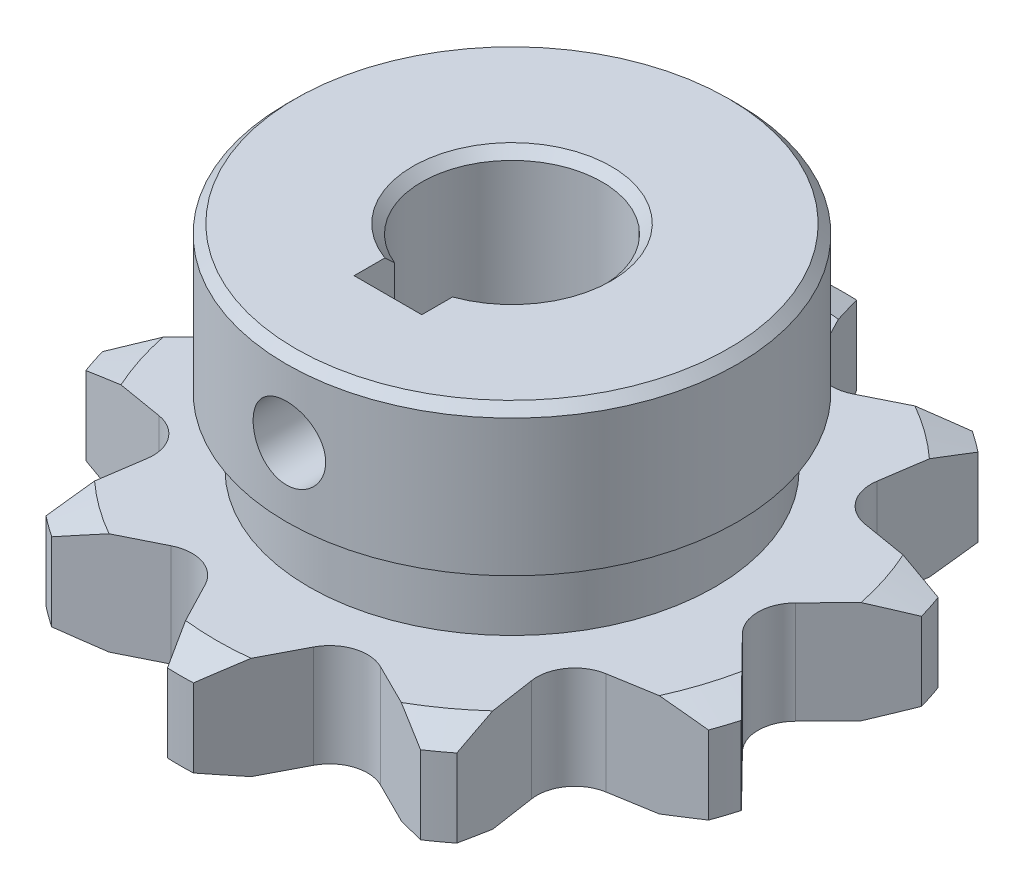
SolidWorks part; units mm, degrees
material "AISI 1045 Acero estirado en frío"
ref_plane "SUPERFICIE" through (0, 0, 0) normal (0, 0, 1) x (1, 0, 0)
ref_plane "FRONTAL" through (0, 0, 0) normal (0, 1, 0) x (1, 0, 0)
ref_plane "LATERAL" through (0, 0, 0) normal (1, 0, 0) x (0, 0, -1)
sketch "Croquis1" plane through (0, 0, 0) normal (0, 1, 0) x (1, 0, 0)
  line L0 (12.9776, 19.4178) -> (7.3685, 16.6238)
  line L1 (14.4571, 18.3429) -> (13.5332, 12.1449)
  line L2 (21.9126, 8.0813) -> (15.7324, 9.1178)
  line L3 (22.4777, 6.342) -> (18.0871, 1.8708)
  line L4 (22.4777, -6.342) -> (18.0871, -1.8708)
  line L5 (-0.9144, 23.3374) -> (-3.81, 17.78)
  line L6 (21.9126, -8.0813) -> (15.7324, -9.1178)
  line L7 (14.4571, -18.3429) -> (13.5332, -12.1449)
  line L8 (0.9144, 23.3374) -> (3.81, 17.78)
  line L9 (12.9776, -19.4178) -> (7.3685, -16.6238)
  line L10 (0.9144, -23.3374) -> (3.81, -17.78)
  line L11 (-0.9144, -23.3374) -> (-3.81, -17.78)
  line L12 (-12.9776, -19.4178) -> (-7.3685, -16.6238)
  line L13 (-14.4571, -18.3429) -> (-13.5332, -12.1449)
  line L14 (-21.9126, -8.0813) -> (-15.7324, -9.1178)
  line L15 (-22.4777, -6.342) -> (-18.0871, -1.8708)
  line L16 (-22.4777, 6.342) -> (-18.0871, 1.8708)
  line L17 (-21.9126, 8.0813) -> (-15.7324, 9.1178)
  line L18 (-14.4571, 18.3429) -> (-13.5332, 12.1449)
  line L19 (-12.9776, 19.4178) -> (-7.3685, 16.6238)
  arc A0 (0.9144, 23.3374) -> (-0.9144, 23.3374) centre (0, 0) ccw
  arc A1 (14.4571, 18.3429) -> (12.9776, 19.4178) centre (0, 0) ccw
  arc A2 (-13.5332, -12.1449) -> (-15.7324, -9.1178) centre (-16.1741, -11.7512) ccw
  arc A3 (-18.0871, -1.8708) -> (-18.0871, 1.8708) centre (-19.9923, 0) ccw
  arc A4 (22.4777, 6.342) -> (21.9126, 8.0813) centre (0, 0) ccw
  arc A5 (-15.7324, 9.1178) -> (-13.5332, 12.1449) centre (-16.1741, 11.7512) ccw
  arc A6 (-7.3685, 16.6238) -> (-3.81, 17.78) centre (-6.178, 19.0138) ccw
  arc A7 (21.9126, -8.0813) -> (22.4777, -6.342) centre (0, 0) ccw
  arc A8 (3.81, 17.78) -> (7.3685, 16.6238) centre (6.178, 19.0138) ccw
  arc A9 (13.5332, 12.1449) -> (15.7324, 9.1178) centre (16.1741, 11.7512) ccw
  arc A10 (12.9776, -19.4178) -> (14.4571, -18.3429) centre (0, 0) ccw
  arc A11 (-3.81, -17.78) -> (-7.3685, -16.6238) centre (-6.178, -19.0138) ccw
  arc A12 (18.0871, 1.8708) -> (18.0871, -1.8708) centre (19.9923, 0) ccw
  arc A13 (-0.9144, -23.3374) -> (0.9144, -23.3374) centre (0, 0) ccw
  arc A14 (15.7324, -9.1178) -> (13.5332, -12.1449) centre (16.1741, -11.7512) ccw
  arc A15 (7.3685, -16.6238) -> (3.81, -17.78) centre (6.178, -19.0138) ccw
  arc A17 (-14.4571, -18.3429) -> (-12.9776, -19.4178) centre (0, 0) ccw
  arc A20 (-22.4777, -6.342) -> (-21.9126, -8.0813) centre (0, 0) ccw
  arc A23 (-21.9126, 8.0813) -> (-22.4777, 6.342) centre (0, 0) ccw
  arc A26 (-12.9776, 19.4178) -> (-14.4571, 18.3429) centre (0, 0) ccw
  point P6 (-0.254, 33.655)
  point P7 (-0.254, 26.67)
  point P8 (0.254, 33.655)
  point P9 (0.254, 26.67)
  point P64 (0, 0)
  point P69 (0.7381, 0)
  point P88 (0, 0)
  point P100 (0.4365, -10.2847)
  dimension "D1" = 23.3553
  dimension "D2" = 0.9144
  dimension "D5" = 1.8288
  dimension "D4" = 10
  dimension "D8" = 17.78
  dimension "D3" = 10
  dimension "D6" = 3.81
  dimension "D7" = 3.81
  dimension "D9" = 17.78
extrude "Saliente-Extruir1" add sketch "Croquis1" along normal blind 7.2136
sketch "Croquis2" plane through (0, 7.2136, 0) normal (0, 1, 0) x (1, 0, 0)
  circle A0 centre (0, 0) radius 15.875
  dimension "D1" = 31.75
extrude "Saliente-Extruir2" add sketch "Croquis2" along normal blind 15.0114
sketch "Croquis3" plane through (0, 0, 0) normal (1, 0, 0) x (0, 0, -1)
  line L0 (0, 0) -> (0, -8.0147) construction
  line L2 (23.9724, 7.2136) -> (23.9724, 6.1468)
  line L5 (23.9724, 7.2136) -> (20.7974, 7.2136)
  line L7 (20.7974, 7.2136) -> (23.9724, 6.1468)
  line L12 (17.78, 7.2136) -> (23.3374, 7.2136) construction
  line L14 (23.3374, 7.2136) -> (23.3374, 0) construction
  dimension "D1" = 1.0668
  dimension "D2" = 0.635
  dimension "D3" = 0
  dimension "D4" = 3.175
revolve "Cortar-Revolución3" cut sketch "Croquis3" angle 360 about L0
ref_plane "Plano1" through (0, 3.6068, 0) normal (0, 1, 0) x (1, 0, 0)
mirror "Simetría1" about plane through (0, 3.6068, 0) normal (0, 1, 0) of "Cortar-Revolución3"
sketch "Croquis5" plane through (0, 22.225, 0) normal (0, 1, 0) x (1, 0, 0)
  circle A0 centre (0, 0) radius 6.35
  dimension "D1" = 12.7
extrude "Cortar-Extruir2" cut sketch "Croquis5" against normal through all
chamfer "Chaflán2" distance 0.635 angle 45 1 edges at (0, 22.225, 15.875)
fillet "Redondeo1" radius 0.635 1 edges at (0, 7.2136, 15.875)
sketch "Croquis8" plane through (0, 0, 0) normal (1, 0, 0) x (0, 0, -1)
  line L0 (0.0045, 0) -> (0.0045, -2.2512) construction
  line L1 (-17.458, 11.9761) -> (-14.283, 11.9761)
  line L2 (-17.458, 11.9761) -> (-17.458, 7.2136)
  line L3 (-17.458, 7.2136) -> (-14.283, 7.2136)
  line L4 (-14.283, 11.9761) -> (-14.283, 7.2136)
  dimension "D1" = 28.575
  dimension "D2" = 4.7625
  dimension "D3" = 3.175
revolve "Cortar-Revolución4" cut sketch "Croquis8" angle 360 about L0
hole_wizard "Taladro roscado 1/4-201" positions "Croquis10" profile "Croquis9" tap size "1/4-20" standard "Ansi Inch"
sketch "Croquis10" plane through (0, 0, 0) normal (0, 0, 1) x (1, 0, 0)
  point P0 (0, 16.783)
sketch "Croquis9" plane through (0, 16.783, 0) normal (1, 0, 0) x (0, 1, 0)
  line L0 (0, 0) -> (0, 15.875)
  line L1 (0, 15.875) -> (2.5527, 15.875)
  line L2 (2.5527, 15.875) -> (2.5527, 0)
  line L5 (2.5527, 0) -> (0, 0)
  line L11 (0, -6.35) -> (0, 107.95) construction
  dimension "Diámetro de perforador para roscar hasta el siguiente" = 5.1054
  dimension "Profundidad de perforador para roscar hasta el siguiente" = 15.875
cosmetic thread "Rosca de taladro1" parameters "D2"=6.35
chamfer "Chaflán3" distance 0.635 angle 45 2 edges at (0, 22.225, 6.35) (0, 0, 6.35)
sketch "Croquis11" plane through (0, 0, 0) normal (0, -1, 0) x (1, 0, 0)
  line L1 (-2.3813, 8.7313) -> (2.3813, 8.7313)
  line L2 (-2.3813, 8.7313) -> (-2.3813, 3.9688)
  line L3 (-2.3813, 3.9688) -> (2.3813, 3.9688)
  line L4 (2.3813, 8.7313) -> (2.3813, 3.9688)
  line L5 (-2.3813, 8.7313) -> (2.3813, 3.9688) construction
  line L6 (-2.3813, 3.9688) -> (2.3813, 8.7313) construction
  circle A0 centre (0, 0) radius 6.35 construction
  point P0 (0, 6.35)
  dimension "D1" = 4.7625
  dimension "D2" = 2.3813
  dimension "D3" = 2.3813
extrude "Cortar-Extruir3" cut sketch "Croquis11" against normal through all
